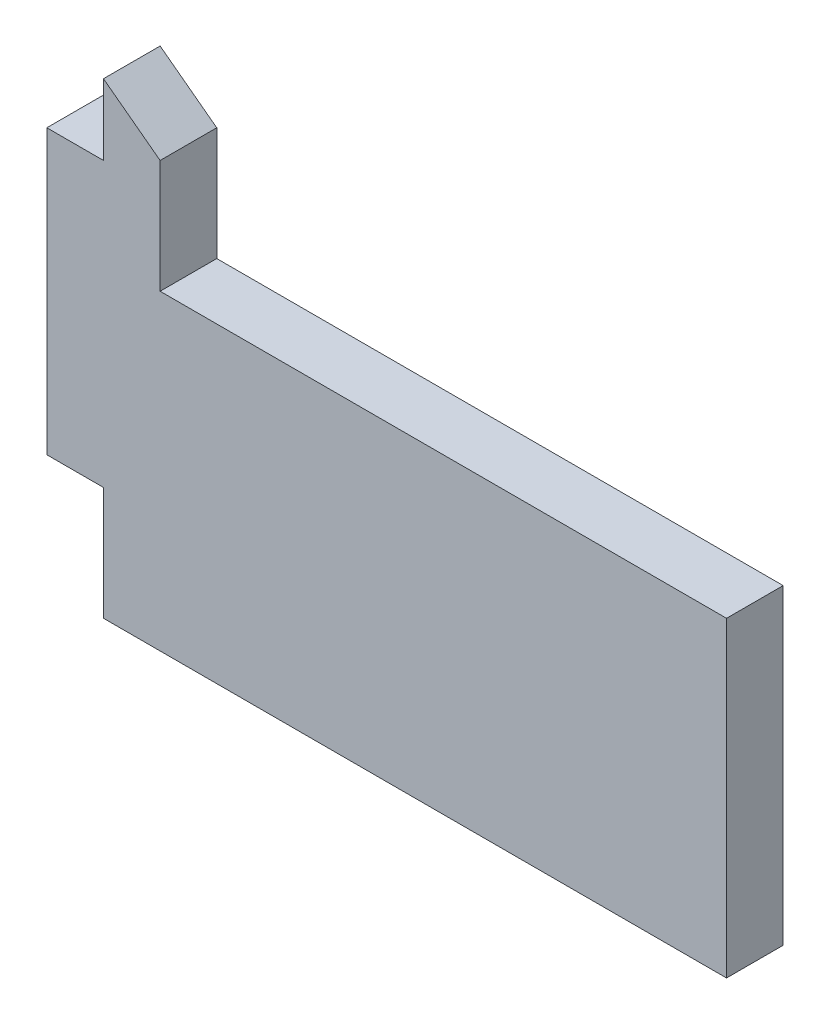
SolidWorks part; units mm, degrees
material "ﾊﾞﾙｻ"
ref_plane "正面" through (0, 0, 0) normal (0, 0, 1) x (1, 0, 0)
ref_plane "平面" through (0, 0, 0) normal (0, 1, 0) x (1, 0, 0)
ref_plane "右側面" through (0, 0, 0) normal (1, 0, 0) x (0, 0, -1)
sketch "ｽｹｯﾁ1" plane through (0, 0, 0) normal (0, 0, 1) x (1, 0, 0)
  line L0 (0, 0) -> (0, 10)
  line L1 (0, 10) -> (2, 10)
  line L2 (2, 10) -> (2, 12.5)
  line L3 (2, 12.5) -> (4, 11)
  line L4 (24, -4) -> (2, -4)
  line L5 (2, -4) -> (2, 0)
  line L6 (2, 0) -> (0, 0)
  line L7 (4, 11) -> (4, 7)
  line L8 (4, 7) -> (24, 7)
  line L9 (24, 7) -> (24, -4)
  line L10 (9.3333, 7) -> (24, -4) construction
  line L11 (4, 11) -> (9.3333, 7) construction
  point P8 (1, 0)
  point P12 (4, 9)
  dimension "D1" = 2
  dimension "D2" = 4
  dimension "D3" = 10
  dimension "D4" = 2.5
  dimension "D5" = 22
  dimension "D6" = 4
  dimension "D7" = 2
extrude "ﾎﾞｽ - 押し出し1" add sketch "ｽｹｯﾁ1" along normal blind 2
